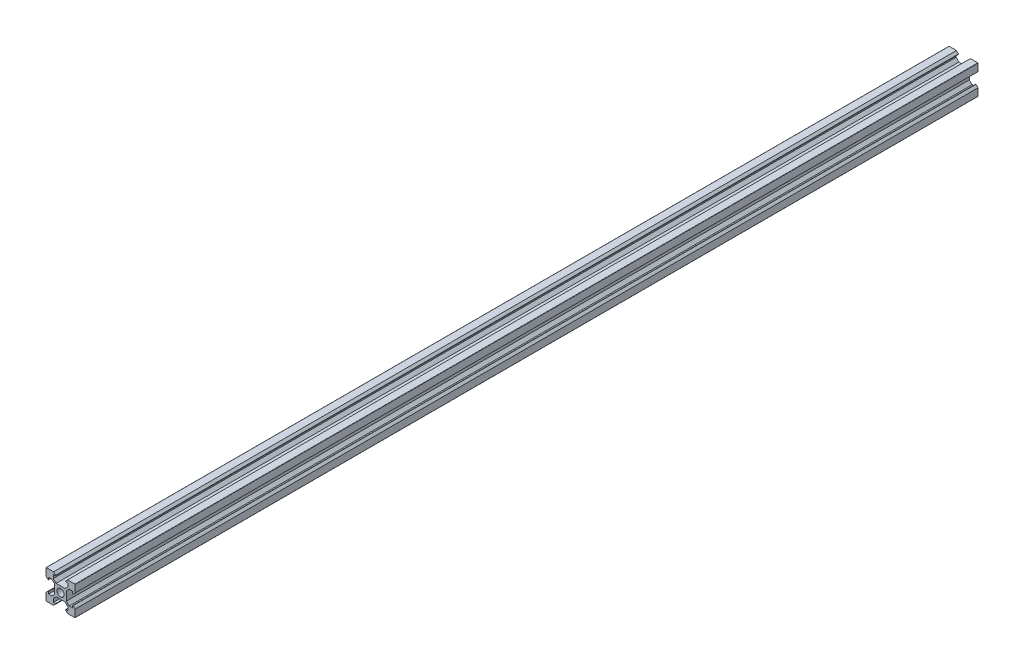
SolidWorks part; units mm, degrees
ref_plane "Front Plane" through (0, 0, 0) normal (0, 0, 1) x (1, 0, 0)
ref_plane "Top Plane" through (0, 0, 0) normal (0, 1, 0) x (1, 0, 0)
ref_plane "Right Plane" through (0, 0, 0) normal (1, 0, 0) x (0, 0, -1)
sketch "Sketch1" plane through (0, 0, 0) normal (0, 0, 1) x (1, 0, 0)
  line L0 (-10, 9.8109) -> (-10, 4.8)
  line L1 (-10, -10) -> (10, -10) construction
  line L2 (-10, -10) -> (-10, 10) construction
  line L3 (-10, 10) -> (10, 10) construction
  line L4 (10, -10) -> (10, 10) construction
  line L5 (-10, -10) -> (10, 10) construction
  line L6 (-10, 10) -> (10, -10) construction
  line L7 (-10, 4.8) -> (-8.6228, 3.4228)
  line L8 (-8.3, 3.5565) -> (-8.3, 5)
  line L9 (-8.3, 5) -> (-5.9192, 5)
  line L10 (-5.9192, 5) -> (-4, 3.0808)
  line L11 (-4, 3.0808) -> (-4, -3.0808)
  line L12 (-9.8109, 10) -> (-4.8, 10)
  line L13 (-3.5565, 8.3) -> (-5, 8.3)
  line L14 (-4.8, 10) -> (-3.4228, 8.6228)
  line L15 (-5, 8.3) -> (-5, 5.9192)
  line L16 (-5, 5.9192) -> (-3.0808, 4)
  line L17 (-3.0808, 4) -> (3.0808, 4)
  line L18 (4, -3.0808) -> (4, 3.0808)
  line L19 (5.9192, -5) -> (4, -3.0808)
  line L20 (8.3, -5) -> (5.9192, -5)
  line L21 (8.3, -3.5565) -> (8.3, -5)
  line L22 (10, -4.8) -> (8.6228, -3.4228)
  line L23 (10, -9.8109) -> (10, -4.8)
  line L24 (9.8109, -10) -> (4.8, -10)
  line L25 (4.8, -10) -> (3.4228, -8.6228)
  line L26 (3.5565, -8.3) -> (5, -8.3)
  line L27 (5, -8.3) -> (5, -5.9192)
  line L28 (5, -5.9192) -> (3.0808, -4)
  line L29 (3.0808, -4) -> (0, -4)
  line L30 (-10, 0) -> (10, 0) construction
  line L31 (-10, -9.8109) -> (-10, -4.8)
  line L32 (-5.9192, -5) -> (-4, -3.0808)
  line L33 (-8.3, -5) -> (-5.9192, -5)
  line L34 (-8.3, -3.5565) -> (-8.3, -5)
  line L35 (-10, -4.8) -> (-8.6228, -3.4228)
  line L36 (0, 10) -> (0, -10) construction
  line L37 (9.8109, 10) -> (4.8, 10)
  line L38 (4.8, 10) -> (3.4228, 8.6228)
  line L39 (3.5565, 8.3) -> (5, 8.3)
  line L40 (5, 8.3) -> (5, 5.9192)
  line L41 (5, 5.9192) -> (3.0808, 4)
  line L42 (10, 9.8109) -> (10, 4.8)
  line L43 (10, 4.8) -> (8.6228, 3.4228)
  line L44 (8.3, 3.5565) -> (8.3, 5)
  line L45 (8.3, 5) -> (5.9192, 5)
  line L46 (5.9192, 5) -> (4, 3.0808)
  line L47 (-3.0808, -4) -> (0, -4)
  line L48 (-5, -5.9192) -> (-3.0808, -4)
  line L49 (-5, -8.3) -> (-5, -5.9192)
  line L50 (-3.5565, -8.3) -> (-5, -8.3)
  line L51 (-4.8, -10) -> (-3.4228, -8.6228)
  line L52 (-9.8109, -10) -> (-4.8, -10)
  circle A0 centre (0, 0) radius 2.5
  arc A1 (8.6228, 3.4228) -> (8.3, 3.5565) centre (8.4891, 3.5565) cw
  arc A2 (-10, 9.8109) -> (-9.8109, 10) centre (-9.8109, 9.8109) cw
  arc A3 (-8.6228, 3.4228) -> (-8.3, 3.5565) centre (-8.4891, 3.5565) ccw
  arc A4 (-3.5565, -8.3) -> (-3.4228, -8.6228) centre (-3.5565, -8.4891) cw
  arc A5 (-8.3, -3.5565) -> (-8.6228, -3.4228) centre (-8.4891, -3.5565) ccw
  arc A6 (-10, -9.8109) -> (-9.8109, -10) centre (-9.8109, -9.8109) ccw
  arc A7 (10, -9.8109) -> (9.8109, -10) centre (9.8109, -9.8109) cw
  arc A8 (3.4228, -8.6228) -> (3.5565, -8.3) centre (3.5565, -8.4891) cw
  arc A9 (8.3, -3.5565) -> (8.6228, -3.4228) centre (8.4891, -3.5565) cw
  arc A10 (9.8109, 10) -> (10, 9.8109) centre (9.8109, 9.8109) cw
  arc A11 (3.4228, 8.6228) -> (3.5565, 8.3) centre (3.5565, 8.4891) ccw
  arc A12 (-3.5565, 8.3) -> (-3.4228, 8.6228) centre (-3.5565, 8.4891) ccw
  point P39 (-4, 0)
  point P45 (0, 4)
  point P51 (4, 0)
  point P58 (8.3, 3.1)
  point P64 (-8.3, 3.1)
  point P67 (-3.1, -8.3)
  point P70 (-8.3, -3.1)
  point P79 (3.1, -8.3)
  point P82 (8.3, -3.1)
  point P88 (3.1, 8.3)
  point P91 (-3.1, 8.3)
  dimension "D1" = 5
  dimension "D8" = 0.1891
  dimension "D2" = 20
  dimension "D3" = 8
  dimension "D4" = 5
  dimension "D5" = 1.7
  dimension "D6" = 1.3
  dimension "D7" = 6.2
extrude "Boss-Extrude5" add sketch "Sketch1" along normal blind 620
